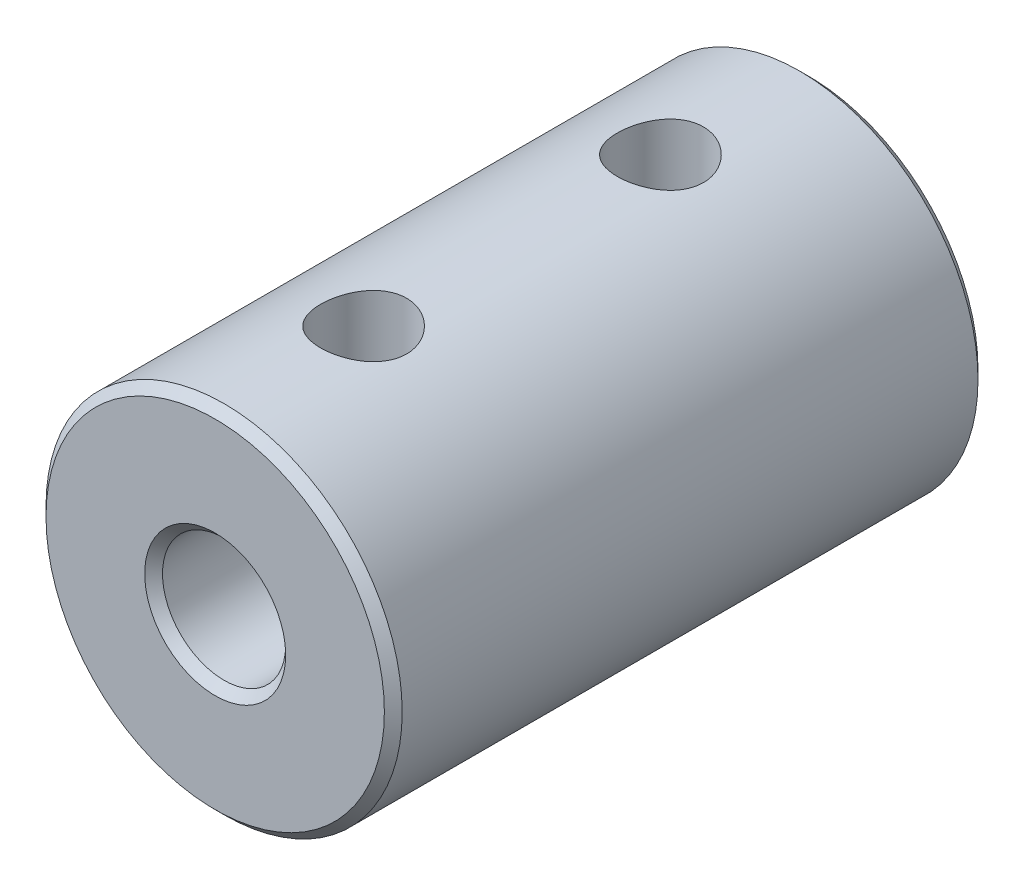
SolidWorks part; units mm, degrees
ref_plane "Plan de face" through (0, 0, 0) normal (0, 0, 1) x (1, 0, 0)
ref_plane "Plan de dessus" through (0, 0, 0) normal (0, 1, 0) x (1, 0, 0)
ref_plane "Plan de droite" through (0, 0, 0) normal (1, 0, 0) x (0, 0, -1)
sketch "Esquisse1" plane through (0, 0, 0) normal (0, 0, 1) x (1, 0, 0)
  circle A0 centre (0, 0) radius 6
  circle A1 centre (0, 0) radius 1.575
extrude "Boss.-Extru.1" add sketch "Esquisse1" along normal mid plane 20
sketch "Esquisse2" plane through (0, 0, 10) normal (0, 0, 1) x (1, 0, 0)
  circle A0 centre (0, 0) radius 2.075
extrude "Enlèv. mat.-Extru.1" cut sketch "Esquisse2" against normal blind 10
ref_plane "Plan1" through (0, 0, 0) normal (0, 1, 0) x (-1, 0, 0)
sketch "Esquisse3" plane through (0, 0, 0) normal (0, 1, 0) x (-1, 0, 0)
  line L0 (0, -2.4446) -> (0, 9.3829) construction
  line L1 (-5.1223, 0) -> (1.4849, 0) construction
  line L2 (-5.1223, 5) -> (1.4849, 5) construction
  circle A0 centre (0, 5) radius 1.45
  circle A1 centre (0, -5) radius 1.45
  dimension "D1" = 5
extrude "Enlèv. mat.-Extru.2" cut sketch "Esquisse3" against normal mid plane 12
chamfer "Chanfrein1" distance 0.3 angle 45 4 edges at (6, 0, -10) (1.575, 0, -10) (2.075, 0, 10) (6, 0, 10)
